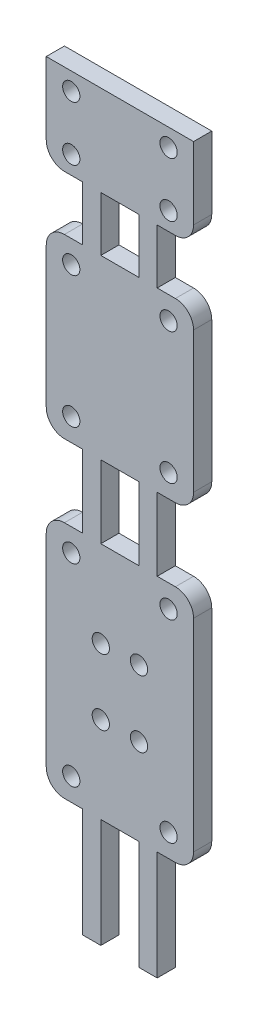
SolidWorks part; units mm, degrees
ref_plane "Front Plane" through (0, 0, 0) normal (0, 0, 1) x (1, 0, 0)
ref_plane "Top Plane" through (0, 0, 0) normal (0, 1, 0) x (1, 0, 0)
ref_plane "Right Plane" through (0, 0, 0) normal (1, 0, 0) x (0, 0, -1)
sketch "Sketch3" plane through (0, 0, 0) normal (0, 0, 1) x (1, 0, 0)
  line L0 (0, 94.0064) -> (0, 86.0614)
  line L1 (16.2, 94.0064) -> (16.2, 86.0614)
  line L2 (0, -0.1536) -> (16.2, -0.1536) construction
  line L3 (0, 76.0614) -> (0, 60.6064)
  line L4 (0, 94.0064) -> (16.2, 94.0064)
  line L5 (0, 12.3464) -> (4, 12.3464) construction
  line L6 (2, 58.6064) -> (4, 58.6064)
  line L7 (16.2, 76.0614) -> (16.2, 60.6064)
  line L8 (0, 48.6064) -> (0, 26.3464)
  line L9 (16.2, 48.6064) -> (16.2, 26.3464)
  line L10 (16.2, 12.3464) -> (16.2, -0.1536) construction
  line L11 (0, 12.3464) -> (0, -0.1536) construction
  line L12 (6, 12.3464) -> (6, 24.3464)
  line L13 (6, 24.3464) -> (10.2, 24.3464)
  line L14 (4, 12.3464) -> (4, 24.3464)
  line L15 (6, 12.3464) -> (10.2, 12.3464) construction
  line L16 (4, 50.6064) -> (4, 58.6064)
  line L17 (4, 78.0614) -> (4, 84.0614)
  line L18 (6, 50.6064) -> (6, 58.6064)
  line L19 (6, 78.0614) -> (6, 84.0614)
  line L20 (6, 84.0614) -> (10.2, 84.0614)
  line L21 (6, 78.0614) -> (10.2, 78.0614)
  line L22 (6, 58.6064) -> (10.2, 58.6064)
  line L23 (6, 50.6064) -> (10.2, 50.6064)
  line L24 (8.1, 94.0064) -> (8.1, -0.1536) construction
  line L25 (12.2, 50.6064) -> (12.2, 58.6064)
  line L26 (2, 50.6064) -> (4, 50.6064)
  line L27 (2, 24.3464) -> (4, 24.3464)
  line L28 (10.2, 12.3464) -> (10.2, 24.3464)
  line L29 (12.2, 12.3464) -> (12.2, 24.3464)
  line L30 (2, 78.0614) -> (4, 78.0614)
  line L31 (10.2, 50.6064) -> (10.2, 58.6064)
  line L32 (2, 84.0614) -> (4, 84.0614)
  line L33 (12.2, 78.0614) -> (12.2, 84.0614)
  line L34 (10.2, 78.0614) -> (10.2, 84.0614)
  line L35 (12.2, 84.0614) -> (14.2, 84.0614)
  line L36 (12.2, 78.0614) -> (14.2, 78.0614)
  line L37 (12.2, 58.6064) -> (14.2, 58.6064)
  line L38 (12.2, 50.6064) -> (14.2, 50.6064)
  line L39 (12.2, 12.3464) -> (16.2, 12.3464) construction
  line L40 (12.2, 24.3464) -> (14.2, 24.3464)
  line L41 (4, 12.3464) -> (6, 12.3464)
  line L42 (10.2, 12.3464) -> (12.2, 12.3464)
  circle A0 centre (6, 33.8464) radius 0.95
  circle A1 centre (10.2, 33.8464) radius 0.95
  circle A2 centre (2.75, 86.0614) radius 0.95
  circle A3 centre (10.2, 41.1664) radius 0.95
  circle A4 centre (13.45, 48.1064) radius 0.95
  circle A5 centre (2.75, 92.0614) radius 0.95
  circle A6 centre (13.45, 86.0614) radius 0.95
  circle A7 centre (2.75, 61.1064) radius 0.95
  arc A8 (14.2, 24.3464) -> (16.2, 26.3464) centre (14.2, 26.3464) ccw
  arc A9 (16.2, 48.6064) -> (14.2, 50.6064) centre (14.2, 48.6064) ccw
  arc A10 (2, 50.6064) -> (0, 48.6064) centre (2, 48.6064) ccw
  arc A11 (0, 26.3464) -> (2, 24.3464) centre (2, 26.3464) ccw
  arc A12 (0, 60.6064) -> (2, 58.6064) centre (2, 60.6064) ccw
  arc A13 (14.2, 58.6064) -> (16.2, 60.6064) centre (14.2, 60.6064) ccw
  arc A14 (16.2, 76.0614) -> (14.2, 78.0614) centre (14.2, 76.0614) ccw
  arc A15 (0, 76.0614) -> (2, 78.0614) centre (2, 76.0614) cw
  circle A16 centre (2.85, 9.8464) radius 0.95 construction
  circle A17 centre (13.35, 9.8464) radius 0.95 construction
  circle A18 centre (13.35, 3.8464) radius 0.95 construction
  circle A19 centre (2.85, 3.8464) radius 0.95 construction
  circle A20 centre (13.45, 61.1064) radius 0.95
  circle A21 centre (2.75, 75.5614) radius 0.95
  circle A22 centre (13.45, 26.8464) radius 0.95
  circle A23 centre (13.45, 75.5614) radius 0.95
  circle A24 centre (13.45, 92.0614) radius 0.95
  circle A25 centre (2.75, 26.8464) radius 0.95
  circle A26 centre (6, 41.1064) radius 0.95
  circle A27 centre (2.75, 48.1064) radius 0.95
  arc A28 (16.2, 86.0614) -> (14.2, 84.0614) centre (14.2, 86.0614) cw
  arc A29 (2, 84.0614) -> (0, 86.0614) centre (2, 86.0614) cw
  point P76 (16.2, 24.3464)
  point P80 (16.2, 50.6064)
  point P84 (0, 50.6064)
  point P88 (0, 24.3464)
  point P95 (0, 58.6064)
  point P99 (16.2, 58.6064)
  point P102 (16.2, 78.0614)
  point P105 (0, 78.0614)
  point P108 (16.2, 84.0614)
  point P111 (0, 84.0614)
  dimension "D1" = 2.5
  dimension "D2" = 9.5
  dimension "D32" = 6
  dimension "D33" = 6
  dimension "D49" = 1.9
  dimension "D50" = 2
  dimension "D3" = 2.5
  dimension "D4" = 9.5
  dimension "D5" = 6
  dimension "D6" = 2.75
  dimension "D7" = 2.75
  dimension "D8" = 6
  dimension "D9" = 2.5
  dimension "D10" = 2.5
  dimension "D11" = 9.5
  dimension "D12" = 9.44
  dimension "D13" = 2.75
  dimension "D14" = 6
  dimension "D15" = 2.75
  dimension "D16" = 6
  dimension "D17" = 12
  dimension "D18" = 2.5
  dimension "D19" = 4
  dimension "D20" = 6
  dimension "D21" = 6
  dimension "D22" = 4
  dimension "D23" = 2.85
  dimension "D24" = 2.85
  dimension "D25" = 26.26
  dimension "D26" = 16.2
  dimension "D27" = 8
  dimension "D28" = 2.5
  dimension "D29" = 2.5
  dimension "D30" = 2.75
  dimension "D31" = 2.75
  dimension "D34" = 2.5
  dimension "D35" = 2.5
  dimension "D36" = 2.75
  dimension "D37" = 2.75
  dimension "D38" = 19.455
  dimension "D39" = 6
  dimension "D40" = 2
  dimension "D41" = 2
  dimension "D42" = 2.75
  dimension "D43" = 2.75
  dimension "D44" = 2.5
  dimension "D45" = 4
  dimension "D46" = 2.75
  dimension "D47" = 2.75
  dimension "D48" = 9.945
extrude "Boss-Extrude3" add sketch "Sketch3" along normal blind 2
sketch "Sketch4" plane through (0, 0, 2) normal (0, 0, 1) x (1, 0, 0)
  line L0 (4, 84.0614) -> (12.2, 84.0614)
  line L1 (12.2, 84.0614) -> (12.2, 78.0614)
  line L2 (12.2, 78.0614) -> (4, 78.0614)
  line L3 (4, 78.0614) -> (4, 84.0614)
  line L4 (4, 58.6064) -> (12.2, 58.6064)
  line L5 (12.2, 58.6064) -> (12.2, 50.6064)
  line L6 (12.2, 50.6064) -> (4, 50.6064)
  line L7 (4, 50.6064) -> (4, 58.6064)
  line L8 (4, 24.3464) -> (12.2, 24.3464)
  line L9 (12.2, 24.3464) -> (12.2, 12.3464)
  line L10 (12.2, 12.3464) -> (4, 12.3464)
  line L11 (4, 12.3464) -> (4, 24.3464)
extrude "Cut-Extrude1" [suppressed] cut sketch "Sketch4" against normal up to surface (2 mm away)
equation "\"D25@Sketch3\"= \"HL@parametersSketch@prostheticParameters.SLDPRT\" * 0.196 - 4 - 6'Index PIP length"
equation "\"D26@Sketch3\"= \"fingerWidth@parametersSketch@prostheticParameters.SLDPRT\"'Index Width"
equation "\"D38@Sketch3\"= \"HL@parametersSketch@prostheticParameters.SLDPRT\" * 0.143 - 3 - 4 'Index MIP Length"
equation "\"D48@Sketch3\"= \"HL@parametersSketch@prostheticParameters.SLDPRT\" * 0.097 - 3 - 5'Index DIP Length - Gap Fingertip"
equation "\"D49@Sketch3\"= 1.5 + \"tol1@parametersSketch@prostheticParameters.SLDPRT\""
